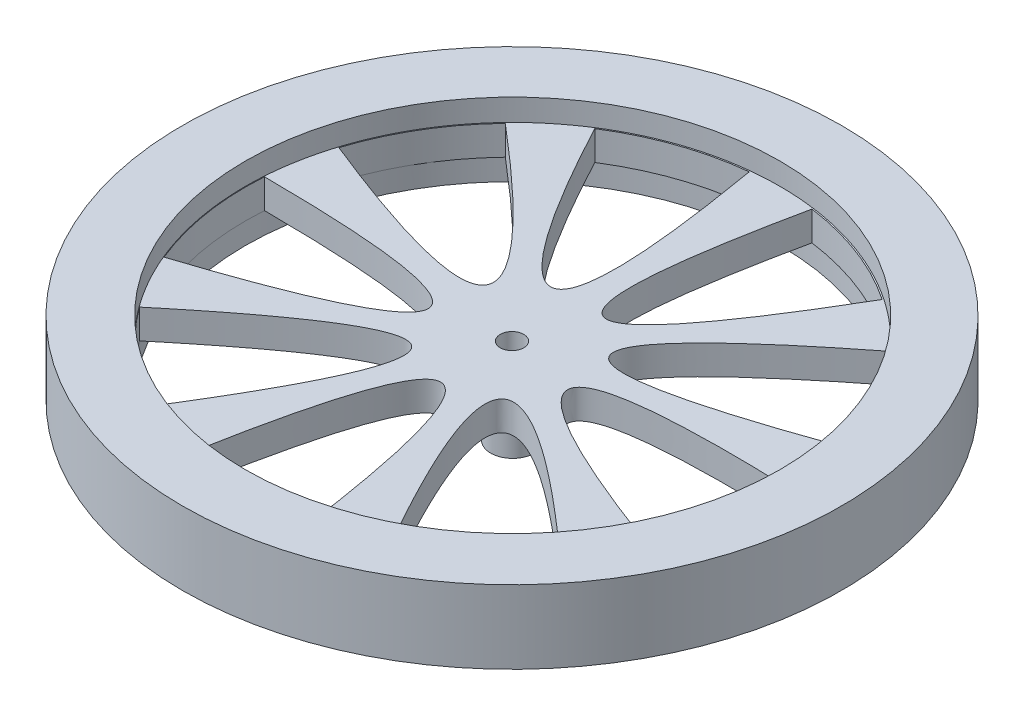
SolidWorks part; units mm, degrees
ref_plane "Front Plane" through (0, 0, 0) normal (0, 0, 1) x (1, 0, 0)
ref_plane "Top Plane" through (0, 0, 0) normal (0, 1, 0) x (1, 0, 0)
ref_plane "Right Plane" through (0, 0, 0) normal (1, 0, 0) x (0, 0, -1)
sketch "Sketch1" plane through (0, 0, 0) normal (0, 1, 0) x (1, 0, 0)
  line L0 (0, 55.5418) -> (0, -55.7193) construction
  line L1 (-76.8358, 0) -> (94.7583, 0) construction
  circle A0 centre (0, -0.0887) radius 45
  circle A1 centre (0, -0.0887) radius 1.6
  dimension "D1" = 90
  dimension "D2" = 3.2
extrude "Boss-Extrude1" add sketch "Sketch1" along normal mid plane 10 contours A0 | A1
sketch "Sketch4" plane through (0, 5, 0) normal (0, 1, 0) x (1, 0, 0)
  circle A0 centre (0, 0) radius 36.5015
sketch "Sketch5" plane through (0, -5, 0) normal (0, -1, 0) x (1, 0, 0)
  circle A0 centre (0, 0) radius 36.5015 construction
  circle A1 centre (0, 0) radius 36.5015
extrude "Cut-Extrude1" cut sketch "Sketch4" against normal blind 3
extrude "Cut-Extrude2" cut sketch "Sketch5" against normal blind 3
sketch "Sketch2" plane through (0, -5, 0) normal (0, -1, 0) x (1, 0, 0)
  circle A0 centre (0, 0) radius 3
  circle A1 centre (0, 0.0887) radius 1.6 construction
  circle A2 centre (0, 0.0887) radius 1.6
  dimension "D1" = 6
extrude "Boss-Extrude2" add sketch "Sketch2" along normal blind 4.8 and the other way blind 4
sketch "Sketch6" plane through (0, -2, 0) normal (0, -1, 0) x (1, 0, 0)
  circle A0 centre (0, 0) radius 36.5015 construction
  circle A1 centre (0, 0) radius 36.5015 construction
  circle A3 centre (0, 0) radius 36.5015
  arc A4 (7.7714, 35.6646) -> (-8.8016, 35.4244) centre (0, 0) ccw
  spline S0 degree 2 poles (-8.8016, 35.4244) (0.4884, -15.9254) (7.7714, 35.6646) knots 0 0 0 1 1 1
  dimension "D1" = 0
extrude "Cut-Extrude3" cut sketch "Sketch6" against normal blind 10 contours S0 A4
pattern_circular "CirPattern1" count 9 over 360 about axis through (0, 5, 0.0887) along (0, -1, 0) of "Cut-Extrude3"
